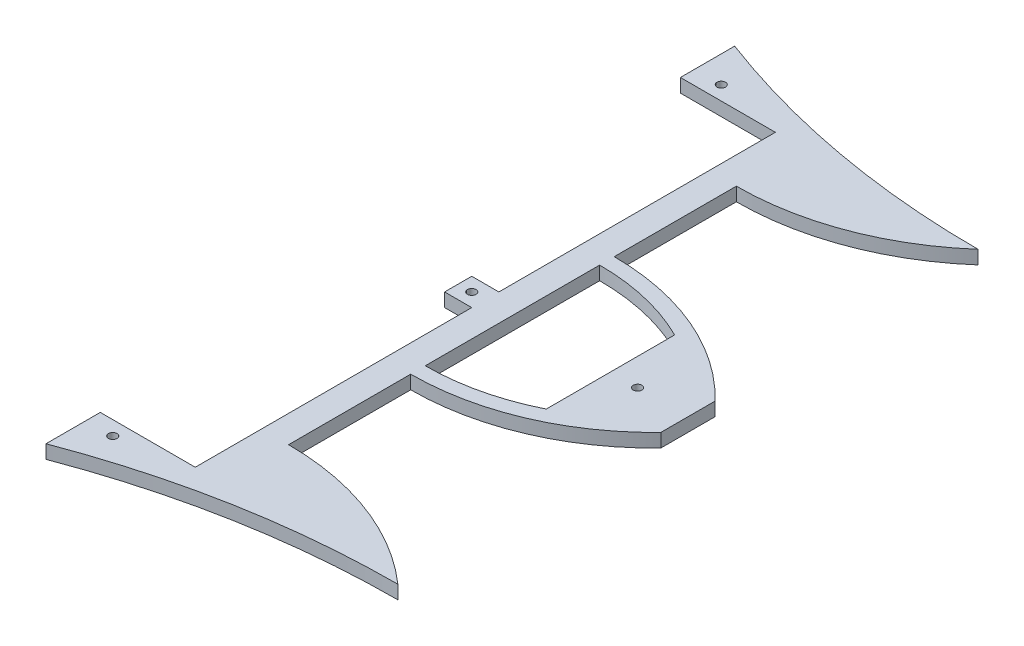
SolidWorks part; units mm, degrees
ref_plane "Front Plane" through (0, 0, 0) normal (0, 0, 1) x (1, 0, 0)
ref_plane "Top Plane" through (0, 0, 0) normal (0, 1, 0) x (1, 0, 0)
ref_plane "Right Plane" through (0, 0, 0) normal (1, 0, 0) x (0, 0, -1)
sketch "Sketch1" plane through (0, 0, 0) normal (0, 1, 0) x (1, 0, 0)
  line L0 (152.4, -101.6) -> (152.4, -50.8)
  line L1 (0, 0) -> (127, 0) construction
  line L2 (133.35, 6.35) -> (133.35, -6.35)
  line L3 (25.4, 0) -> (25.4, 38.1)
  line L4 (25.4, 38.1) -> (25.4, 114.3)
  line L5 (146.05, 6.35) -> (146.05, 112.1634)
  line L6 (101.6, 161.1449) -> (101.6, 135.7449)
  line L7 (101.6, -135.7449) -> (124.4369, -135.7449)
  line L8 (0, 0) -> (152.4, 0) construction
  line L9 (101.6, 63.5) -> (152.4, 63.5) construction
  line L10 (101.6, -135.7449) -> (101.6, -161.1449)
  line L11 (152.4, 50.8) -> (190.0762, 12.7)
  line L12 (146.05, -6.35) -> (146.05, -112.1634)
  line L13 (101.6, 135.7449) -> (124.4369, 135.7449)
  line L14 (161.1449, 101.6) -> (202.8194, 101.6)
  line L15 (152.4, 50.8) -> (152.4, 101.6)
  line L16 (152.4, 101.6) -> (157.6874, 106.8874)
  line L17 (152.4, -101.6) -> (157.6874, -106.8874)
  line L18 (152.4, -50.8) -> (190.0762, -12.7)
  line L19 (124.4369, 135.7449) -> (190.5, 135.7449)
  line L20 (146.05, 76.2) -> (158.75, 76.2)
  line L21 (158.75, 76.2) -> (158.75, 101.6)
  line L22 (158.75, 76.2) -> (158.75, 50.8)
  line L23 (133.35, -6.35) -> (146.05, -6.35)
  line L24 (190.0762, 12.7) -> (240.8762, 12.7)
  line L25 (240.8762, 12.7) -> (240.8762, 135.7449)
  line L26 (190.5, 135.7449) -> (240.8762, 135.7449)
  line L27 (101.6, -63.5) -> (152.4, -63.5) construction
  line L28 (133.35, 6.35) -> (146.05, 6.35)
  line L29 (190.5, -135.7449) -> (240.8762, -135.7449)
  line L30 (240.8762, -12.7) -> (240.8762, -135.7449)
  line L31 (190.0762, -12.7) -> (240.8762, -12.7)
  line L32 (158.75, -76.2) -> (158.75, -50.8)
  line L33 (158.75, -76.2) -> (158.75, -101.6)
  line L34 (146.05, -76.2) -> (158.75, -76.2)
  line L35 (124.4369, -135.7449) -> (190.5, -135.7449)
  line L36 (152.4, -101.6) -> (157.6874, -106.8874)
  line L37 (152.4, -50.8) -> (152.4, -101.6)
  line L38 (161.1449, -101.6) -> (202.8194, -101.6)
  line L39 (152.4, -50.8) -> (190.0762, -12.7)
  line L40 (146.05, 101.6) -> (101.6, 101.6)
  line L41 (101.6, 101.6) -> (101.6, 135.7449)
  line L42 (146.05, -101.6) -> (101.6, -101.6)
  line L43 (101.6, -101.6) -> (101.6, -135.7449)
  line L44 (240.8762, 12.7) -> (240.8762, -12.7)
  arc A0 (152.4, 114.3) -> (152.4, -114.3) centre (0, 0) ccw construction
  arc A1 (146.05, 112.1634) -> (124.4369, 135.7449) centre (0, 0) ccw construction
  arc A2 (101.6, -161.1449) -> (152.4, -114.3) centre (0, 0) ccw
  arc A3 (124.4369, -135.7449) -> (146.05, -112.1634) centre (0, 0) ccw
  arc A4 (146.05, 112.1634) -> (124.4369, 135.7449) centre (0, 0) ccw
  arc A5 (152.4, 114.3) -> (101.6, 161.1449) centre (0, 0) ccw
  arc A6 (116.785, 142.3815) -> (101.6, -153.586) centre (0, 0) ccw construction
  arc A7 (124.4369, -135.7449) -> (146.05, -112.1634) centre (0, 0) ccw construction
  arc A8 (157.6874, 106.8874) -> (161.1449, 101.6) centre (0, 0) ccw construction
  arc A9 (157.6874, 106.8874) -> (152.4, 114.3) centre (0, 0) ccw
  arc A10 (190.0762, -12.7) -> (190.0762, 12.7) centre (0, 0) ccw
  arc A11 (157.6874, -106.8874) -> (152.4, -114.3) centre (0, 0) cw
  arc A12 (158.75, 50.8) -> (240.8762, 12.7) centre (158.75, -56.7633) cw
  arc A13 (158.75, 101.6) -> (240.8762, 135.7449) centre (158.75, 217.4384) ccw
  arc A14 (157.6874, -106.8874) -> (161.1449, -101.6) centre (0, 0) cw construction
  arc A15 (158.75, -101.6) -> (240.8762, -135.7449) centre (158.75, -217.4384) cw
  arc A16 (158.75, -50.8) -> (240.8762, -12.7) centre (158.75, 56.7633) ccw
  arc A17 (157.6874, -106.8874) -> (152.4, -114.3) centre (0, 0) cw
  arc A18 (152.4, -114.3) -> (101.6, -161.1449) centre (0, 0) cw
  point P37 (101.6, 63.5)
  point P67 (101.6, -63.5)
  point P91 (0, 0)
  dimension "D24" = 50.8
  dimension "D10" = 25.4
  dimension "D6" = 127
  dimension "D5" = 381
  dimension "D9" = 368.3
  dimension "D2" = 25.4
  dimension "D3" = 38.1
  dimension "D4" = 76.2
  dimension "D7" = 152.4
  dimension "D8" = 6.35
  dimension "D11" = 22.8369
  dimension "D12" = 25.4
  dimension "D13" = 12.7
  dimension "D14" = 12.7
  dimension "D15" = 50.8
  dimension "D16" = 63.5
  dimension "D17" = 50.8
  dimension "D18" = 12.7
  dimension "D19" = 12.7
  dimension "D20" = 12.7
  dimension "D21" = 25.4
  dimension "D22" = 25.4
  dimension "D23" = 66.0631
extrude "Boss-Extrude3" add sketch "Sketch1" along normal blind 6.35 contours L10 A2 L35 L7 | L7 A3 L12 L42 L43 | A15 L33 L34 L0 L17 A11 A2 L35 L29 | L18 A10 L11 L15 L20 L5 L28 L2 L23 L12 L34 L0 | A11 L17 L0 L34 L12 A3 L35 A2 | L5 A4 L13 L41 L40 | L19 A5 L6 L13 | L16 A9 A5 L19 A4 L5 L20 L15 | A12 L22 L20 L15 L11 L24 | L32 A16 L31 L18 L0 L34 | A10 L31 L44 L24 | L21 A13 L26 L19 A5 A9 L16 L15 L20
sketch "Sketch2" plane through (0, 6.35, 0) normal (0, 1, 0) x (1, 0, 0)
  line L0 (44.5421, 0) -> (0, 0)
  line L1 (0, 0) -> (126.5613, 142.3815)
  line L2 (126.5613, 142.3815) -> (114.0807, 142.3815)
  circle A0 centre (139.7, 0) radius 2
  arc A1 (133.6546, 135.7449) -> (101.6, 161.1449) centre (0, 0) ccw construction
  circle A2 centre (114.0807, 142.3815) radius 2
  circle A3 centre (114.0807, -142.3815) radius 2
  dimension "D1" = 4
  dimension "D4" = 4
  dimension "D2" = 48.366
  dimension "D3" = 12.4806
extrude "Cut-Extrude1" cut sketch "Sketch2" against normal blind 6.35
sketch "Sketch3" plane through (0, 6.35, 0) normal (0, 1, 0) x (1, 0, 0)
  line L0 (133.6546, 135.7449) -> (240.8762, 135.7449) construction
  line L1 (101.6, 101.6) -> (146.05, 101.6)
  line L2 (101.6, 101.6) -> (101.6, 135.7449)
  line L3 (101.6, 135.7449) -> (146.05, 135.7449)
  line L4 (146.05, 101.6) -> (146.05, 135.7449)
  line L5 (133.6546, -135.7449) -> (240.8762, -135.7449) construction
  line L6 (101.6, -101.6) -> (146.05, -101.6)
  line L7 (101.6, -101.6) -> (101.6, -135.7449)
  line L8 (101.6, -135.7449) -> (146.05, -135.7449)
  line L9 (146.05, -101.6) -> (146.05, -135.7449)
extrude "Cut-Extrude2" cut sketch "Sketch3" against normal blind 6.35
sketch "Sketch4" plane through (0, 6.35, 0) normal (0, 1, 0) x (1, 0, 0)
  line L0 (240.8762, 135.7449) -> (101.6, 135.7449)
  line L1 (101.6, 135.7449) -> (101.6, 161.1449)
  line L2 (0, 0) -> (19.3108, 0)
  line L3 (240.8762, -135.7449) -> (101.6, -135.7449)
  line L4 (101.6, -135.7449) -> (101.6, -161.1449)
  line L5 (101.6, -161.1449) -> (133.6546, -135.7449)
  line L6 (101.6, 161.1449) -> (133.6546, 135.7449)
  arc A0 (240.8762, 135.7449) -> (101.6, 161.1449) centre (240.8762, 530.2925) cw
  arc A1 (240.8762, -135.7449) -> (101.6, -161.1449) centre (240.8762, -530.2925) ccw
  line M3 (146.05, -135.7449) -> (240.8762, -135.7449)
  line M11 (240.8762, 135.7449) -> (146.05, 135.7449)
extrude "Boss-Extrude5" add sketch "Sketch4" against normal blind 6.35 contours A0 L6 L0 M11 | A1 L3 L5 M3
sketch "Sketch6" plane through (0, 6.35, 0) normal (0, 1, 0) x (1, 0, 0)
  line L0 (158.75, 40.8112) -> (158.75, -40.8112)
  line L1 (240.8762, 12.7) -> (240.8762, -12.7) construction
  line L2 (204.6038, 30.046) -> (204.6038, -30.046)
  arc A0 (158.75, -40.8112) -> (240.8762, 0) centre (158.75, 62.2275) ccw
  arc A1 (158.75, 40.8112) -> (240.8762, 0) centre (158.75, -62.2275) cw
extrude "Cut-Extrude3" cut sketch "Sketch6" against normal blind 6.35 contours A1 L0 A0 L2
sketch "Sketch7" plane through (0, 6.35, 0) normal (0, 1, 0) x (1, 0, 0)
  line L0 (133.8859, 104.775) -> (158.75, 104.775)
  line L1 (158.75, 101.6) -> (119.552, 101.6)
  line L2 (158.75, 104.775) -> (158.75, 101.6)
  line L3 (158.75, 50.8) -> (127.773, 50.8)
  line L4 (127.773, 47.625) -> (158.75, 47.625)
  line L5 (158.75, 50.8) -> (158.75, 47.625)
  line L6 (0, 0) -> (34.1221, 0)
  line L7 (158.75, -50.8) -> (158.75, -47.625)
  line L8 (127.773, -47.625) -> (158.75, -47.625)
  line L9 (158.75, -50.8) -> (127.773, -50.8)
  line L10 (158.75, -104.775) -> (158.75, -101.6)
  line L11 (158.75, -101.6) -> (119.552, -101.6)
  line L12 (133.8859, -104.775) -> (158.75, -104.775)
  arc A0 (158.75, 104.775) -> (240.8762, 135.7449) centre (158.75, 229.1513) ccw
  arc A1 (158.75, 47.625) -> (240.8762, 12.7) centre (158.75, -66.3974) cw
  arc A2 (158.75, -47.625) -> (240.8762, -12.7) centre (158.75, 66.3974) ccw
  arc A3 (158.75, -104.775) -> (240.8762, -135.7449) centre (158.75, -229.1513) cw
  arc M9 (240.8762, -135.7449) -> (158.75, -101.6) centre (158.75, -217.4384) ccw
  arc M11 (158.75, -50.8) -> (240.8762, -12.7) centre (158.75, 56.7633) ccw
  arc M13 (240.8762, 12.7) -> (158.75, 50.8) centre (158.75, -56.7633) ccw
  arc M15 (158.75, 101.6) -> (240.8762, 135.7449) centre (158.75, 217.4384) ccw
  dimension "D1" = 3.175
  dimension "D2" = 3.175
extrude "Cut-Extrude4" cut sketch "Sketch7" against normal blind 6.35 contours A0 L2 M15 | L5 A1 M13 | A2 L7 M11 | L10 A3 M9
sketch "Sketch8" plane through (0, 6.35, 0) normal (0, 1, 0) x (1, 0, 0)
  line L0 (204.6038, 30.046) -> (204.6038, -30.046) construction
  circle A0 centre (217.3038, 0) radius 2
  dimension "D1" = 12.7
  dimension "D2" = 4
extrude "Cut-Extrude5" cut sketch "Sketch8" against normal blind 6.35
